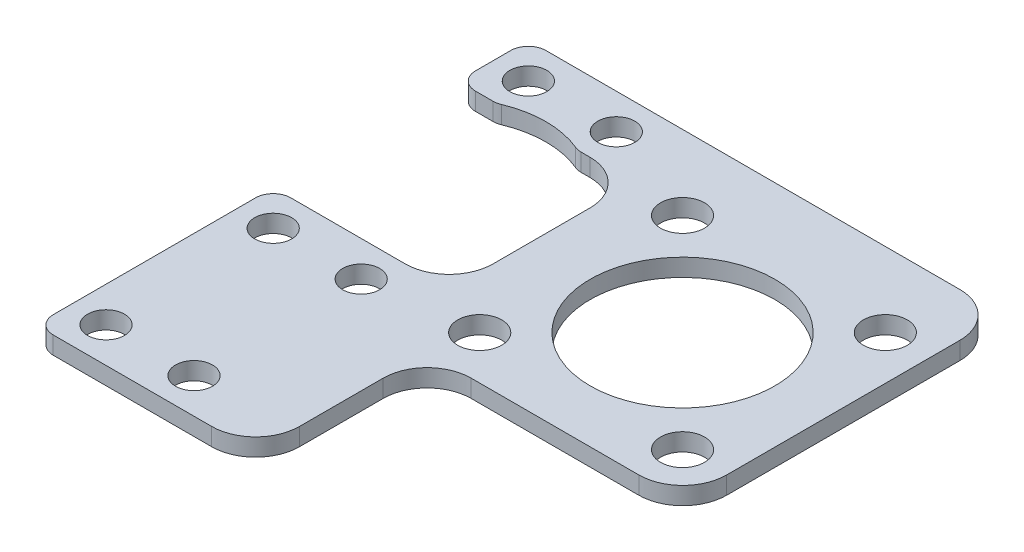
SolidWorks part; units mm, degrees
material "A-Glass Fiber"
ref_plane "Front Plane" through (0, 0, 0) normal (0, 0, 1) x (1, 0, 0)
ref_plane "Top Plane" through (0, 0, 0) normal (0, 1, 0) x (1, 0, 0)
ref_plane "Right Plane" through (0, 0, 0) normal (1, 0, 0) x (0, 0, -1)
sketch "Sketch1" plane through (0, 0, 0) normal (0, 1, 0) x (1, 0, 0)
  line L0 (-11.5258, 11.5258) -> (11.5258, -11.5258) construction
  line L1 (-11.5258, 11.5258) -> (11.5258, 11.5258) construction
  line L2 (-11.5258, 11.5258) -> (-11.5258, -11.5258) construction
  line L3 (-11.5258, -11.5258) -> (11.5258, -11.5258) construction
  line L4 (11.5258, 11.5258) -> (11.5258, -11.5258) construction
  line L5 (-35.5258, 12) -> (-33.5258, 12)
  line L6 (-33.5258, 16) -> (-23.5258, 16) construction
  line L7 (-33.5258, 16) -> (-33.5258, -32) construction
  line L8 (-33.5258, -32) -> (-23.5258, -32) construction
  line L9 (-23.5258, 16) -> (-23.5258, -32) construction
  line L10 (-17.5258, 7) -> (-17.5258, -4)
  line L11 (-22.5258, -9) -> (-35.5258, -9)
  line L12 (-37.5258, -11) -> (-37.5258, -34)
  line L13 (-35.5258, -36) -> (-17.5258, -36)
  line L14 (-12.5258, -31) -> (-12.5258, -21.5)
  line L15 (-7.5258, -16.5) -> (11.5258, -16.5)
  line L16 (-37.5258, 14) -> (-37.5258, 18)
  line L18 (16.5258, -11.5) -> (16.5258, 15)
  line L19 (0, 16.5) -> (0, -16.5) construction
  line L23 (-28.5258, 21.7017) -> (-28.5258, -19.4127) construction
  line L24 (-23.5258, 12) -> (-22.5258, 12)
  line L25 (-35.5258, 20) -> (11.5258, 20)
  circle A1 centre (-11.5258, 11.5258) radius 2.5
  circle A2 centre (11.5258, 11.5258) radius 2.5
  circle A3 centre (11.5258, -11.5258) radius 2.5
  circle A4 centre (-11.5258, -11.5258) radius 2.5
  circle A5 centre (-33.5258, 16) radius 2.1
  circle A6 centre (-23.5258, 16) radius 2.1
  circle A7 centre (-33.5258, -32) radius 2.1
  circle A8 centre (-23.5258, -32) radius 2.1
  arc A9 (-17.5258, -36) -> (-12.5258, -31) centre (-17.5258, -31) ccw
  arc A10 (-12.5258, -21.5) -> (-7.5258, -16.5) centre (-7.5258, -21.5) cw
  arc A11 (11.5258, -16.5) -> (16.5258, -11.5) centre (11.5258, -11.5) ccw
  arc A12 (11.5258, 20) -> (16.5258, 15) centre (11.5258, 15) cw
  arc A13 (-37.5258, 18) -> (-35.5258, 20) centre (-35.5258, 18) cw
  arc A14 (-35.5258, 12) -> (-37.5258, 14) centre (-35.5258, 14) cw
  arc A15 (-35.5258, -9) -> (-37.5258, -11) centre (-35.5258, -11) ccw
  arc A16 (-37.5258, -34) -> (-35.5258, -36) centre (-35.5258, -34) ccw
  circle A19 centre (-33.5258, -13) radius 2.1
  circle A20 centre (-23.5258, -13) radius 2.1
  arc A21 (-22.5258, 12) -> (-17.5258, 7) centre (-22.5258, 7) cw
  arc A22 (-17.5258, -4) -> (-22.5258, -9) centre (-22.5258, -4) cw
  circle A23 centre (0, 0) radius 10.5
  circle A26 centre (-28.5258, 2) radius 10 construction
  arc A27 (-32.7566, 12.1538) -> (-24.2951, 12.1538) centre (-28.5258, 2) cw
  arc A28 (-24.2951, 12.1538) -> (-23.5258, 12) centre (-23.5258, 14) ccw
  arc A29 (-32.7566, 12.1538) -> (-33.5258, 12) centre (-33.5258, 14) cw
  point P21 (-23.5258, -8)
  point P42 (-12.5258, -16.5)
  point P45 (16.5258, -16.5)
  point P53 (-37.5258, 12)
  point P56 (-37.5258, -9)
  point P77 (-23.9433, 12)
  dimension "D2" = 21
  dimension "D3" = 5
  dimension "D4" = 4.2
  dimension "D14" = 5
  dimension "D15" = 2
  dimension "D18" = 5
  dimension "D24" = 20
  dimension "D25" = 11
  dimension "D26" = 2
  dimension "D1" = 32.6
  dimension "D5" = 10
  dimension "D6" = 48
  dimension "D7" = 12
  dimension "D8" = 10
  dimension "D9" = 4
  dimension "D10" = 4
  dimension "D11" = 11
  dimension "D12" = 5
  dimension "D13" = 5
  dimension "D16" = 15
  dimension "D17" = 11
  dimension "D19" = 4
  dimension "D20" = 16.5
  dimension "D21" = 2
  dimension "D27" = 14
extrude "Boss-Extrude1" add sketch "Sketch1" along normal blind 2
